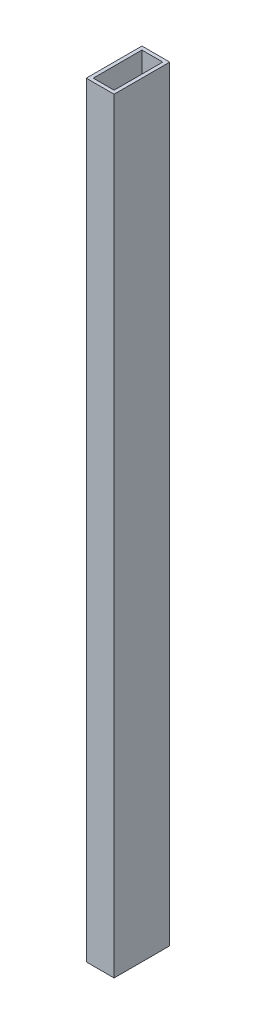
SolidWorks part; units mm, degrees
material "1060 Alloy"
ref_plane "Front Plane" through (0, 0, 0) normal (0, 0, 1) x (1, 0, 0)
ref_plane "Top Plane" through (0, 0, 0) normal (0, 1, 0) x (1, 0, 0)
ref_plane "Right Plane" through (0, 0, 0) normal (1, 0, 0) x (0, 0, -1)
sketch "Sketch1" plane through (0, 0, 0) normal (0, 1, 0) x (1, 0, 0)
  line L0 (3.175, 47.625) -> (22.225, 47.625)
  line L1 (0, 0) -> (25.4, 0)
  line L2 (0, 0) -> (0, 50.8)
  line L3 (0, 50.8) -> (25.4, 50.8)
  line L4 (25.4, 0) -> (25.4, 50.8)
  line L5 (22.225, 3.175) -> (22.225, 47.625)
  line L6 (3.175, 3.175) -> (22.225, 3.175)
  line L7 (3.175, 3.175) -> (3.175, 47.625)
  dimension "D2" = 50.8
  dimension "D3" = 25.4
  dimension "D1" = 3.175
extrude "Boss-Extrude1" add sketch "Sketch1" along normal blind 698.5
